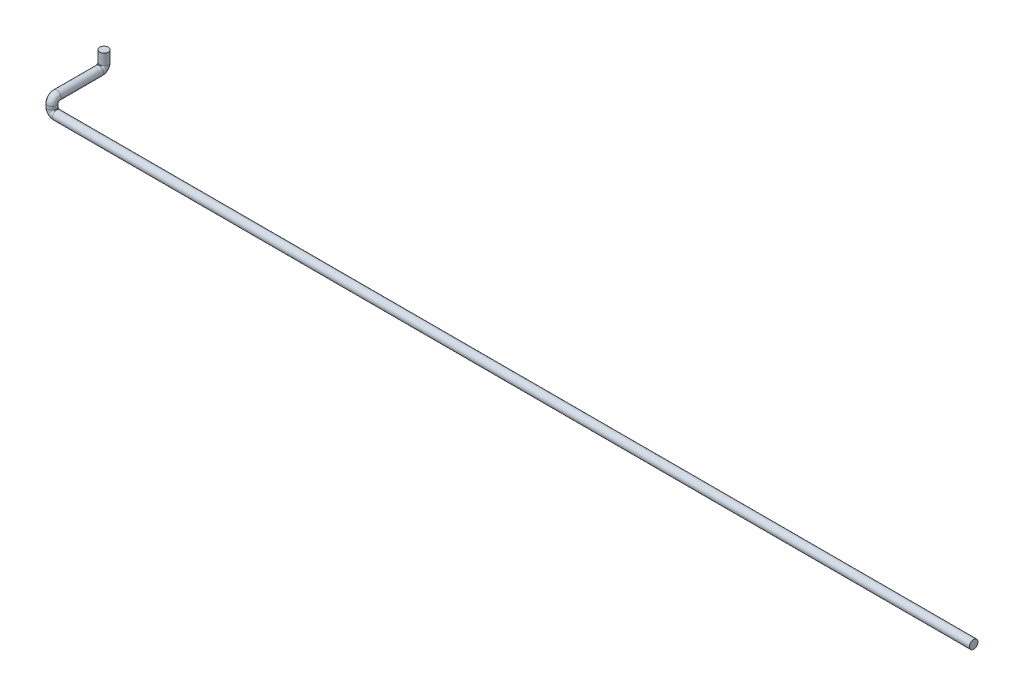
SolidWorks part; units mm, degrees
ref_plane "Alzado" through (0, 0, 0) normal (0, 0, 1) x (1, 0, 0)
ref_plane "Planta" through (0, 0, 0) normal (0, 1, 0) x (1, 0, 0)
ref_plane "Vista lateral" through (0, 0, 0) normal (1, 0, 0) x (0, 0, -1)
sketch3d "Croquis3D1"
  line L0 (0, 0, 0) -> (-2930, 0, 0)
  line L1 (-2945, 15, 0) -> (-2945, 25, 0)
  line L2 (-2945, 40, -15) -> (-2945, 40, -151)
  line L3 (-2945, 55, -166) -> (-2945, 90, -166)
  arc A0 (-2945, 40, -151) -> (-2945, 55, -166) centre (-2945, 55, -151) ccw
  arc A1 (-2945, 25, 0) -> (-2945, 40, -15) centre (-2945, 25, -15) ccw
  arc A2 (-2930, 0, 0) -> (-2945, 15, 0) centre (-2930, 15, 0) ccw
  point P8 (-2945, 40, -166)
  point P9 (-2930, 55, -151)
  point P12 (-2945, 40, 0)
  point P13 (-2960, 25, -15)
  point P16 (-2945, 0, 0)
  point P17 (-2930, 15, -15)
  dimension "D5" = 15
  dimension "D1" = 2945
  dimension "D2" = 40
  dimension "D3" = 166
  dimension "D4" = 50
sketch "Croquis1" plane through (0, 0, 0) normal (1, 0, 0) x (0, 0, -1)
  circle A0 centre (0, 0) radius 13.7
  dimension "D1" = 27.4
sweep "Barrer1" add profiles "Croquis1" path "Croquis3D1"
